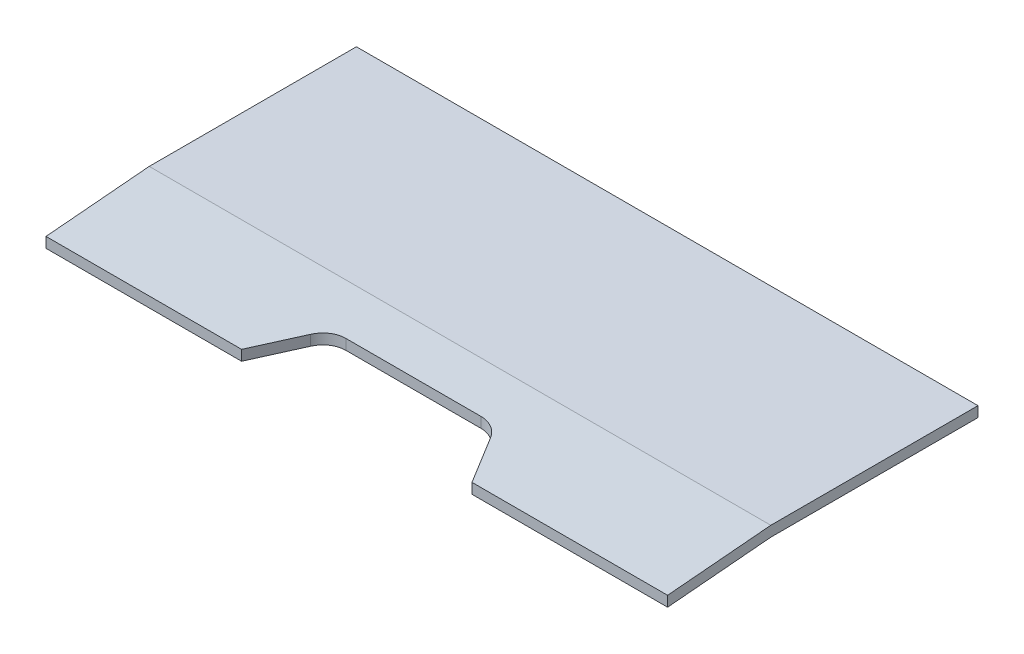
SolidWorks part; units mm, degrees
ref_plane "Спереди" through (0, 0, 0) normal (0, 0, 1) x (1, 0, 0)
ref_plane "Сверху" through (0, 0, 0) normal (0, 1, 0) x (1, 0, 0)
ref_plane "Справа" through (0, 0, 0) normal (1, 0, 0) x (0, 0, -1)
sketch "Эскиз2" plane through (0, 0, 0) normal (1, 0, 0) x (0, 0, -1)
  line L5 (0, 20) -> (0, 0)
  line L6 (-599.2389, -17.4311) -> (-599.2389, 2.5689)
  line L7 (-400, 0) -> (-599.2389, -17.4311)
  line L8 (-599.2389, 2.5689) -> (-400, 20)
  line L9 (-400, 20) -> (0, 20)
  line L10 (0, 0) -> (-400, 0)
extrude "Бобышка-Вытянуть1" add sketch "Эскиз2" against normal blind 1200
sketch "Эскиз3" plane through (0, 20, 0) normal (0, 1, 0) x (1, 0, 0)
  line L0 (-600, 31.6284) -> (-600, -615.4416) construction
  line L1 (-822.3857, -599.2389) -> (-377.6143, -599.2389)
  line L2 (-1200, -599.2389) -> (0, -599.2389) construction
  line L3 (-822.3857, -599.2389) -> (-773.5489, -514.8351)
  line L4 (-730.2712, -489.8759) -> (-469.7288, -489.8759)
  line L5 (-377.6143, -599.2389) -> (-426.4511, -514.8351)
  arc A0 (-426.4511, -514.8351) -> (-469.7288, -489.8759) centre (-469.7288, -539.8759) ccw
  arc A1 (-773.5489, -514.8351) -> (-730.2712, -489.8759) centre (-730.2712, -539.8759) cw
  point P9 (-600, -489.8759)
  point P10 (-600, -599.2389)
  point P12 (-440.8927, -489.8759)
  point P15 (-759.1073, -489.8759)
  dimension "D1" = 50
extrude "Вырез-Вытянуть1" cut sketch "Эскиз3" against normal through all
